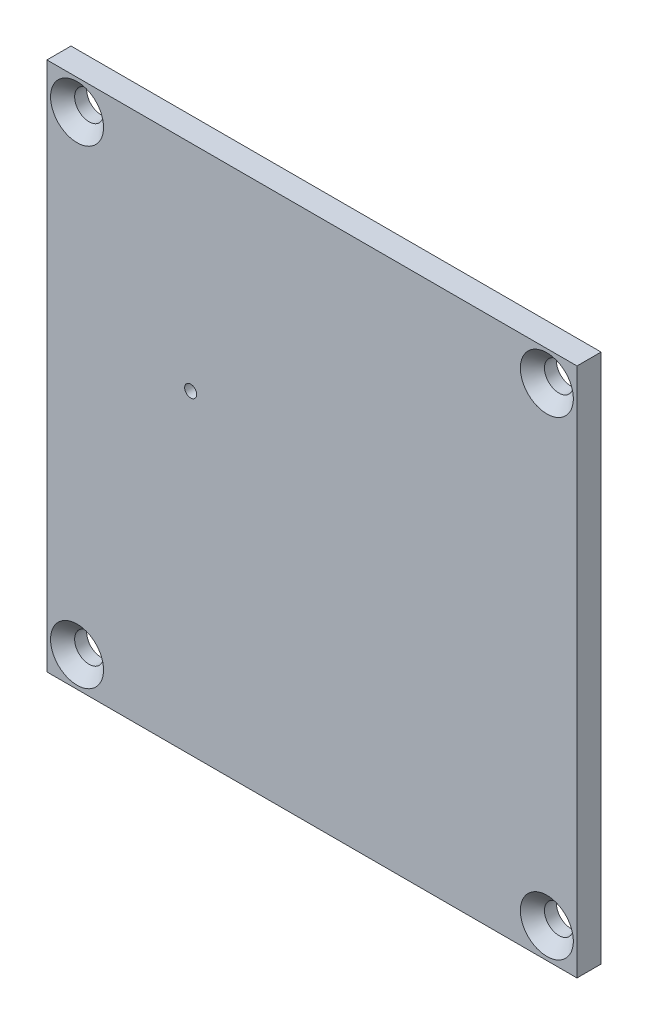
SolidWorks part; units mm, degrees
ref_plane "Plan de face" through (0, 0, 0) normal (1, 0, 0) x (0, 1, 0)
ref_plane "Plan de dessus" through (0, 0, 0) normal (0, 0, 1) x (0, 1, 0)
ref_plane "Plan de droite" through (0, 0, 0) normal (0, 1, 0) x (-1, 0, 0)
sketch "Esquisse3" plane through (0, 0, 0) normal (0, 0, 1) x (0, 1, 0)
  line L1 (-22, -22) -> (22, -22)
  line L2 (-22, -22) -> (-22, 22)
  line L3 (-22, 22) -> (22, 22)
  line L4 (22, -22) -> (22, 22)
  line L5 (-22, -22) -> (22, 22) construction
  line L6 (-22, 22) -> (22, -22) construction
  point P0 (0, 0)
extrude "Boss.-Extru.1" add sketch "Esquisse3" along normal blind 2
sketch "Sketch_Holes" plane through (0, 0, 2) normal (0, 0, 1) x (1, 0, 0)
  circle A0 centre (-10.0677, 4.1602) radius 0.5
extrude "Cut_Extrude_Holes" cut sketch "Sketch_Holes" against normal through all
hole_wizard "Fraisage pour vis à tête fraisée M21" positions "Esquisse4" profile "Esquisse5" countersink size "M2" standard "Ansi Metric" end condition through all
sketch "Esquisse4" plane through (0, 0, 2) normal (0, 0, 1) x (1, 0, 0)
  line L4 (-22, 22) -> (-22, -22) construction
  line L5 (22, 22) -> (-22, 22) construction
  line L6 (22, -22) -> (22, 22) construction
  line L7 (-22, -22) -> (22, -22) construction
  point P2 (19.5, -19.5)
  point P19 (-19.5, -19.5)
  point P21 (-19.5, 19.5)
  point P23 (19.5, 19.5)
  dimension "D3" = 41.5
  dimension "D4" = 41.5
sketch "Esquisse5" plane through (19.5, -19.5, 2) normal (1, 0, 0) x (0, -1, 0)
  line L0 (0, 0) -> (0, 2)
  line L1 (0, 2) -> (1.2, 2)
  line L2 (1.2, 2) -> (1.2, 1)
  line L3 (1.2, 1) -> (2.2, 0)
  line L5 (2.2, 0) -> (0, 0)
  line L6 (-1.2, 1) -> (-2.2, 0) construction
  line L11 (0, -6.35) -> (0, 107.95) construction
  dimension "Diamètre du perçage jusqu'au prochain" = 2.4
  dimension "Profondeur du perçage jusqu'au prochain" = 2
  dimension "Diamètre du fraisage entrant" = 4.4
  dimension "Angle du fraisage entrant" = 90
equation "\"Plaque_L\"=\"Cavite_L\"+\"Cavite_E\"'longueur plaque"
equation "\"Plaque_H\"= \"Cavite_L\"+\"Cavite_E\"'largeur plaque"
equation "\"Plaque_E\"= 2mm'épaisseur plaque superieure et inferieure"
equation "\"Trou_R\"= 1.2mm'rayon perforation base"
equation "\"Trou_dx\"= 4mm'distance entre trou sur x"
equation "\"Trou-dy\"= 4mm'distance entre trou sur y"
equation "\"Cavite_H\"= 18mm'hauteur cavité"
equation "\"Cavite_L\"=\"Cavite_largeur\"+\"Cavite_E\"'longueur cavité"
equation "\"Cavite_E\"= 3mm'épaisseur cavité"
equation "\"Offset_Z\"= 0mm"
equation "\"D1@Esquisse3\"=\"largeur_plaque_enveloppe\""
equation "\"D2@Esquisse3\"=\"largeur_plaque_enveloppe\""
equation "\"D1@Boss.-Extru.1\"=\"Plaque_E\""
equation "\"N_Plaque\"= 7"
equation "\"N_Cavite\"= 6"
equation "\"Cavite_largeur\"= 28mm'largeur cavité"
equation "\"Offset_cavite\"= \"Cavite_E\" / 2"
equation "\"Offset_hauteur_vis1\"= \"Cavite_E\""
equation "\"Offset_hauteur_vis2\"= \"Cavite_H\" - \"Cavite_E\""
equation "\"H_total\"=113mm'122-2*2"
equation "\"espace_vis\"=22.6mm'"
equation "\"Largeur_equerre_enveloppe\"=\"Cavite_L\"+\"Cavite_E\""
equation "\"Enveloppe_E\"=5mm"
equation "\"Offset_Enveloppe\"= \"Enveloppe_E\" / 2"
equation "\"Longueur_equerre_enveloppe\"=\"Cavite_L\"+\"Cavite_E\"+\"Enveloppe_E\""
equation "\"largeur_plaque_enveloppe\"=\"Longueur_equerre_enveloppe\"+\"Enveloppe_E\""
equation "\"D1@Esquisse4\"=\"largeur_plaque_enveloppe\"-\"Offset_Enveloppe\""
equation "\"D2@Esquisse4\"=\"largeur_plaque_enveloppe\"-\"Offset_Enveloppe\""
equation "\"D3@Esquisse4\"=\"largeur_plaque_enveloppe\"-\"Offset_Enveloppe\""
equation "\"D4@Esquisse4\"=\"largeur_plaque_enveloppe\"-\"Offset_Enveloppe\""
